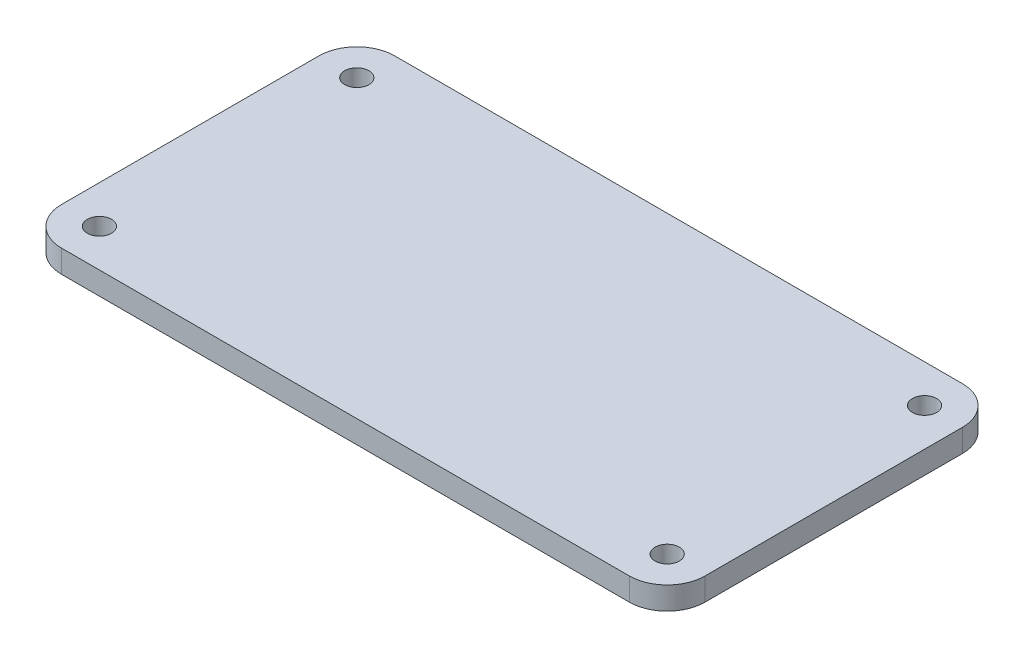
SolidWorks part; units mm, degrees
ref_plane "前视基准面" through (0, 0, 0) normal (0, 0, 1) x (1, 0, 0)
ref_plane "上视基准面" through (0, 0, 0) normal (0, 1, 0) x (1, 0, 0)
ref_plane "右视基准面" through (0, 0, 0) normal (1, 0, 0) x (0, 0, -1)
other "Configuration Table"
sketch "草图1" plane through (0, 0, 0) normal (0, 1, 0) x (1, 0, 0)
  line L1 (42.5, -22) -> (-42.5, -22)
  line L2 (42.5, -22) -> (42.5, 22)
  line L3 (42.5, 22) -> (-42.5, 22)
  line L4 (-42.5, -22) -> (-42.5, 22)
  line L5 (42.5, -22) -> (-42.5, 22) construction
  line L6 (42.5, 22) -> (-42.5, -22) construction
  point P0 (0, 0)
  dimension "D1" = 85
  dimension "D2" = 44
extrude "凸台-拉伸1" add sketch "草图1" along normal blind 3
sketch "草图2" plane through (0, 3, 0) normal (0, 1, 0) x (1, 0, 0)
  line L0 (42.5, 22) -> (-42.5, 22) construction
  line L1 (-42.5, 22) -> (-42.5, -22) construction
  line L2 (-42.5, -22) -> (42.5, -22) construction
  line L3 (42.5, -22) -> (42.5, 22) construction
  circle A0 centre (-37.5, 17) radius 1.6
  circle A1 centre (-37.5, -17) radius 1.6
  circle A2 centre (37.5, 17) radius 1.6
  circle A3 centre (37.5, -17) radius 1.6
  dimension "D1" = 3.2
  dimension "D2" = 3.2
  dimension "D3" = 3.2
  dimension "D4" = 3.2
  dimension "D6" = 5
  dimension "D7" = 5
  dimension "D8" = 5
  dimension "D9" = 5
  dimension "D10" = 5
  dimension "D11" = 5
  dimension "D12" = 5
  dimension "D5" = 5
extrude "切除-拉伸1" cut sketch "草图2" against normal through all
fillet "圆角1" radius 5 4 edges at (42.5, 1.5, -22) (42.5, 1.5, 22) (-42.5, 1.5, 22) (-42.5, 1.5, -22)
